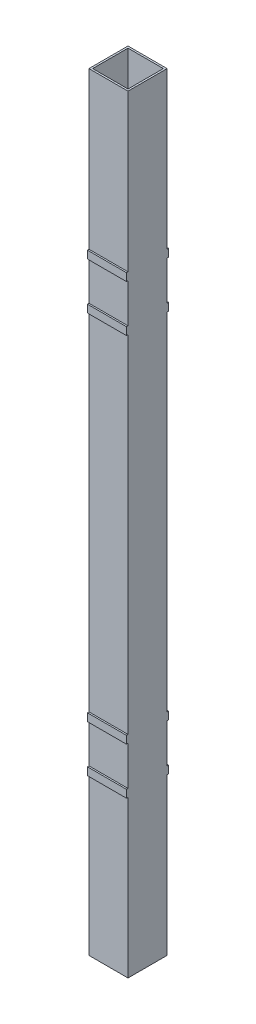
SolidWorks part; units mm, degrees
ref_plane "Alzado" through (0, 0, 0) normal (0, 0, 1) x (1, 0, 0)
ref_plane "Planta" through (0, 0, 0) normal (0, 1, 0) x (1, 0, 0)
ref_plane "Vista lateral" through (0, 0, 0) normal (1, 0, 0) x (0, 0, -1)
sketch "Sketch1" plane through (0, 0, 0) normal (0, 1, 0) x (1, 0, 0)
  line L0 (0, 0) -> (25.4, 0)
  line L1 (25.4, 0) -> (25.4, 25.4)
  line L2 (25.4, 25.4) -> (0, 25.4)
  line L3 (0, 25.4) -> (0, 0)
  line L4 (1.2, 24.2) -> (1.2, 1.2)
  line L5 (1.2, 1.2) -> (24.2, 1.2)
  line L6 (24.2, 1.2) -> (24.2, 24.2)
  line L7 (24.2, 24.2) -> (1.2, 24.2)
  dimension "D1" = 25.4
  dimension "D2" = 25.4
  dimension "D3" = 1.2
  dimension "D4" = 1.2
  dimension "D5" = 1.2
  dimension "D6" = 1.2
extrude "Boss-Extrude1" add sketch "Sketch1" along normal blind 499.2
sketch "Sketch3" plane through (0, 0, -25.4) normal (0, 0, -1) x (-1, 0, 0)
  line L0 (-25.4, 392.5) -> (0, 392.5)
  line L1 (-25.4, 499.2) -> (-25.4, 0) construction
  line L2 (0, 499.2) -> (0, 0) construction
  line L3 (0, 392.5) -> (0, 367.1)
  line L4 (0, 367.1) -> (-25.4, 367.1)
  line L5 (-25.4, 367.1) -> (-25.4, 392.5)
  line L6 (-25.4, 132.1) -> (0, 132.1)
  line L7 (0, 132.1) -> (0, 106.7)
  line L8 (0, 106.7) -> (-25.4, 106.7)
  line L9 (-25.4, 106.7) -> (-25.4, 132.1)
  line L11 (-25.4, 106.7) -> (-25.4, 101.7)
  line L12 (-25.4, 101.7) -> (0, 101.7)
  line L13 (0, 101.7) -> (0, 106.7)
  line L14 (-25.4, 132.1) -> (-25.4, 137.1)
  line L15 (-25.4, 137.1) -> (0, 137.1)
  line L16 (0, 137.1) -> (0, 132.1)
  line L17 (-25.4, 392.5) -> (-25.4, 397.5)
  line L18 (-25.4, 397.5) -> (0, 397.5)
  line L19 (0, 397.5) -> (0, 392.5)
  line L20 (0, 367.1) -> (0, 362.1)
  line L21 (0, 362.1) -> (-25.4, 362.1)
  line L22 (-25.4, 362.1) -> (-25.4, 367.1)
  line L23 (-25.4, 0) -> (0, 0) construction
  line M8 (0, 0) -> (0, 499.2)
  line M10 (-25.4, 499.2) -> (-25.4, 0)
  dimension "D1" = 25.4
  dimension "D2" = 25.4
  dimension "D3" = 235
  dimension "D4" = 101.7
  dimension "D5" = 5
  dimension "D6" = 5
  dimension "D7" = 5
  dimension "D8" = 5
extrude "Boss-Extrude2" add sketch "Sketch3" along normal blind 1 and the other way blind 26.4 contours L12 L8 M10 M8 | L15 L6 M10 M8 | L18 L0 M10 M8 | L21 L4 M8 M10
